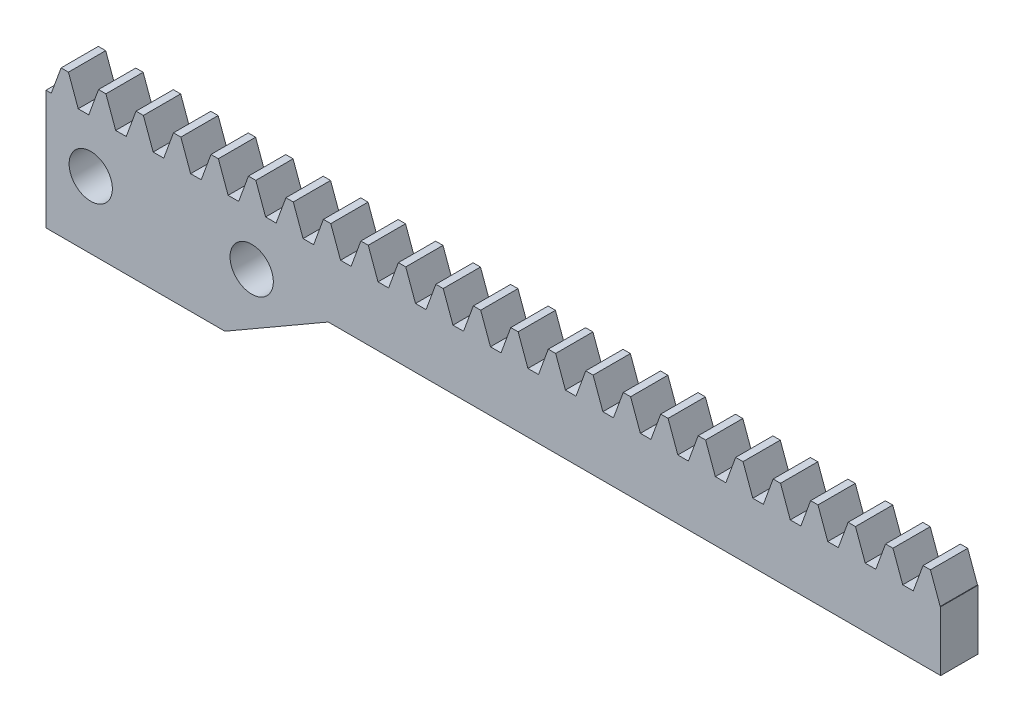
SolidWorks part; units mm, degrees
extrude "Blank" add sketch "BlankSke" against normal blind 2.5
sketch "BlankSke" plane through (0, 0, 0) normal (0, 0, 1) x (1, 0, 0)
  line L1 (0, 0) -> (60, 0)
  line L2 (0, 0) -> (0, 5.8)
  line L3 (0, 5.8) -> (60, 5.8)
  line L4 (60, 0) -> (60, 5.8)
  dimension "Length" = 60
  dimension "Blank_height" = 5.8
ref_plane "Plane1" through (0, 0, 0) normal (0, 0, 1) x (1, 0, 0)
ref_plane "Plane2" through (0, 0, 0) normal (0, 1, 0) x (1, 0, 0)
ref_plane "Plane3" through (0, 0, 0) normal (1, 0, 0) x (0, 0, -1)
sketch "HoldingSke" plane through (0, 0, 0) normal (0, 1, 0) x (1, 0, 0)
  line L0 (0, 0) -> (0.174, 1.2378)
  line L1 (-15, 0) -> (100, 0) construction
  line L2 (0, 0) -> (-2.1039, 2.3779)
  line L3 (0, 0) -> (-11.863, 4.5341)
  line L4 (0, 0) -> (7.8269, 3.6497)
  line L5 (0, 0) -> (-23.7986, -8.8762)
  line L6 (0, 0) -> (-10.5278, -7.1032)
  line L9 (-71.009, 38.7566) -> (-14.6274, 59.2778)
  line L10 (-76.2, 3.1779) -> (-71.2, 3.1779)
  line L11 (0, 0) -> (-2.5, 0)
  line L12 (-76.2, 101.6) -> (-76.17, 101.6)
  line L13 (24.9733, 27.94) -> (52.9518, 28.4284)
  line L14 (24.9733, 27.94) -> (24.9743, 27.94)
  line L15 (24.9733, 27.94) -> (100.4006, 29.5858)
  circle A0 centre (0, 0) radius 19.05
  circle A1 centre (0, 0) radius 2.5
  circle A2 centre (0, 0) radius 12.7
  dimension "MPH" = 5
  dimension "Diameter" = 38.1
  dimension "Num_teeth" = 25
  dimension "Pitch" = 1.25
  dimension "Show_teeth" = 998
  dimension "Thickness" = 12.7
  dimension "Ap" = 20
  dimension "Pitch_height" = 5
  dimension "Width" = 2.5
  dimension "Backlash" = 0.03
  dimension "Addendum_fac" = 1
  dimension "Dedendum_fac" = 1.25
  dimension "Clearance_fac" = 0.25
  dimension "Dedendum_add" = 0.001
  dimension "Length" = 60
  dimension "Module" = 0.8
sketch "TooCutSkeIll" plane through (0, 0, 0) normal (0, 0, 1) x (1, 0, 0)
  line L0 (-1.0018, 5.7789) -> (-0.4025, 4.1323)
  line L1 (-0.2136, 4) -> (0.2136, 4)
  line L2 (0.4025, 4.1323) -> (1.0018, 5.7789)
  line L3 (60, 5.8) -> (0, 5.8) construction
  line L4 (0, 0) -> (0, 64.897) construction
  line L5 (-13.208, 5) -> (12.954, 5) construction
  line L6 (0, 0) -> (60, 0) construction
  line L7 (0.7183, 5) -> (0.7183, 48.7463) construction
  line L8 (-0.7183, 5) -> (-0.7183, 48.7463) construction
  line L9 (1.0319, 5.8) -> (1.0319, 5.8254)
  line L10 (-1.0319, 5.8) -> (-1.0319, 5.8254)
  line L11 (-1.0319, 5.8254) -> (1.0319, 5.8254)
  arc A0 (0.2136, 4) -> (0.4025, 4.1323) centre (0.2136, 4.201) ccw
  arc A1 (-0.4025, 4.1323) -> (-0.2136, 4) centre (-0.2136, 4.201) ccw
  arc A2 (1.0319, 5.8) -> (1.0018, 5.7789) centre (1.0319, 5.768) ccw
  arc A3 (-1.0018, 5.7789) -> (-1.0319, 5.8) centre (-1.0319, 5.768) ccw
  dimension "Pitch_height" = 5
  dimension "Addendum_plus" = 0.8254
  dimension "Pressure_angle" = 20
  dimension "Gap_width" = 1.4366
  dimension "Dedendum" = 1
extrude "ToothCutIll" [suppressed] cut sketch "TooCutSkeIll" against normal through all
sketch "TooCutSkeSim" plane through (0, 0, 0) normal (0, 0, 1) x (1, 0, 0)
  line L0 (0.3543, 4) -> (-0.3543, 4)
  line L1 (1.0187, 5.8254) -> (0.3543, 4)
  line L2 (0, 17.4625) -> (0, 53.467) construction
  line L3 (1.0187, 5.8254) -> (-1.0187, 5.8254)
  line L6 (-1.0187, 5.8254) -> (-0.3543, 4)
  line L9 (-0.7183, 5) -> (0.7183, 5) construction
  line L10 (0, 0) -> (60, 0) construction
  line L11 (0.7183, 5) -> (0.7183, 53.467) construction
  line L12 (-0.7183, 5) -> (-0.7183, 53.467) construction
  dimension "Pitch_height" = 5
  dimension "Addendum_plus" = 0.8254
  dimension "Pressure_angle" = 20
  dimension "Gap_width" = 1.4366
  dimension "Dedendum" = 1
extrude "ToothCutSim" cut sketch "TooCutSkeSim" against normal through all
pattern_linear "TeethCuts" count 25 spacing 2.5133 along (1, 0, 0) of "ToothCutIll", "ToothCutSim"
sketch "草图2" plane through (0, 0, -2.5) normal (0, 0, -1) x (-1, 0, 0)
  line L0 (0, 4) -> (0, -4)
  line L1 (0, -4) -> (-12, -4)
  line L2 (-12, -4) -> (-18.9282, 0)
  line L3 (0, 0) -> (-60, 0) construction
  line L4 (-18.9282, 0) -> (0, 4)
  dimension "D1" = 4
  dimension "D2" = 150
  dimension "D3" = 12
extrude "凸台-拉伸1" add sketch "草图2" against normal blind 2.5
sketch "草图3" plane through (0, 0, -2.5) normal (0, 0, -1) x (-1, 0, 0)
  line L0 (-3, 0.5) -> (-13.7942, 0.5) construction
  line L1 (-18.9282, 0) -> (-12, -4) construction
  line L2 (0, 4) -> (0, -4) construction
  line L3 (-12, -4) -> (0, -4) construction
  circle A0 centre (-3, 0.5) radius 1.45
  circle A1 centre (-13.7942, 0.5) radius 1.45
  circle A2 centre (-13.7942, 0.5) radius 3 construction
  circle A3 centre (-3, 0.5) radius 3 construction
  dimension "D1" = 2.9
  dimension "D2" = 6
  dimension "D3" = 4.5
extrude "切除-拉伸1" cut sketch "草图3" against normal blind 12 and the other way blind 23
equation "' \"Module@HoldingSke\" = 6.35"
equation "' \"Num_teeth@HoldingSke\" = 12"
equation "' \"Ap@HoldingSke\" =  20"
equation "' \"Ap@HoldingSke\" = 20"
equation "' \"Width@HoldingSke\" = 0.25 * 25.4"
equation "' \"Show_teeth@HoldingSke\" = 500"
equation "' \"Backlash@HoldingSke\" = 0.009 * 25.4"
equation "' \"Addendum_fac@HoldingSke\" = 1.0"
equation "' \"Dedendum_fac@HoldingSke\" = 1.25"
equation "' \"Dedendum_add@HoldingSke\" = 0.00005 * 25.4"
equation "' \"Clearance_fac@HoldingSke\" = 0.25"
equation "' \"Pitch_height@HoldingSke\" = 1 * 25.4"
equation "' \"Length@HoldingSke\" = 4.71 * 25.4"
equation "\"Pitch@HoldingSke\" = 1 / \"Module@HoldingSke\""
equation "\"MPH@HoldingSke\" = \"Dedendum_fac@HoldingSke\" / \"Pitch@HoldingSke\" + 2 * \"Dedendum_add@HoldingSke\" + 0.002 * 25.4"
equation "\"MPH@HoldingSke\" = ((sgn( \"MPH@HoldingSke\" - \"Pitch_height@HoldingSke\")+1)*( \"MPH@HoldingSke\" - \"Pitch_height@HoldingSke\"))/2 + \"Pitch_height@HoldingSke\""
equation "\"Blank_height@BlankSke\" = \"Pitch_height@HoldingSke\" + \"Addendum_fac@HoldingSke\"  / \"Pitch@HoldingSke\" "
equation "\"Length@BlankSke\" =  \"Length@HoldingSke\""
equation "\"Face_width@Blank\" = \"Width@HoldingSke\""
equation "\"Pressure_angle@TooCutSkeIll\" = \"Ap@HoldingSke\""
equation "\"Addendum_plus@TooCutSkeIll\" =  \"Addendum_fac@HoldingSke\"  / \"Pitch@HoldingSke\" + 0.001 *25.4"
equation "\"Dedendum@TooCutSkeIll\" = \"Dedendum_fac@HoldingSke\"  / \"Pitch@HoldingSke\""
equation "\"Pitch_height@TooCutSkeIll\" =  \"MPH@HoldingSke\""
equation "\"Gap_width@TooCutSkeIll\" = 3.14159265 / 2 / \"Pitch@HoldingSke\" + 6 * \"Backlash@HoldingSke\""
equation "\"Pressure_angle@TooCutSkeSim\" = \"Ap@HoldingSke\""
equation "\"Addendum_plus@TooCutSkeSim\" =  \"Addendum_fac@HoldingSke\"  / \"Pitch@HoldingSke\" + 0.001 * 25.4"
equation "\"Dedendum@TooCutSkeSim\" = \"Dedendum_fac@HoldingSke\"  / \"Pitch@HoldingSke\""
equation "\"Pitch_height@TooCutSkeSim\" =  \"MPH@HoldingSke\""
equation "\"Gap_width@TooCutSkeSim\" = 3.14159265 / 2 / \"Pitch@HoldingSke\" + 6 * \"Backlash@HoldingSke\""
equation "\"Root_fillet@TooCutSkeIll\" = \"Clearance_fac@HoldingSke\" / \"Pitch@HoldingSke\" + \"Dedendum_add@HoldingSke\""
equation "\"Break_rad@TooCutSkeIll\" = 0.02 / \"Pitch@HoldingSke\" * 2"
equation "\"Linear_pitch@TeethCuts\" = 3.14159265 / \"Pitch@HoldingSke\""
equation "\"Num_teeth@HoldingSke\" = int( ( \"Length@HoldingSke\" + 0 ) / (3.14159265 / \"Pitch@HoldingSke\")) + 0.9999  + 1"
equation " \"Num_teeth@TeethCuts\" = int( \"Show_teeth@HoldingSke\" ) + 1"
equation " \"Num_teeth@TeethCuts\" = ((sgn( \"Num_teeth@TeethCuts\" - \"Num_teeth@HoldingSke\" )-1)*( \"Num_teeth@TeethCuts\" - \"Num_teeth@HoldingSke\" ))/-2+ \"Num_teeth@HoldingSke\""
equation " \"Num_teeth@TeethCuts\" = ((sgn( \"Num_teeth@TeethCuts\" - 2.0)+1)*( \"Num_teeth@TeethCuts\" - 2.0))/2 +2.0"
